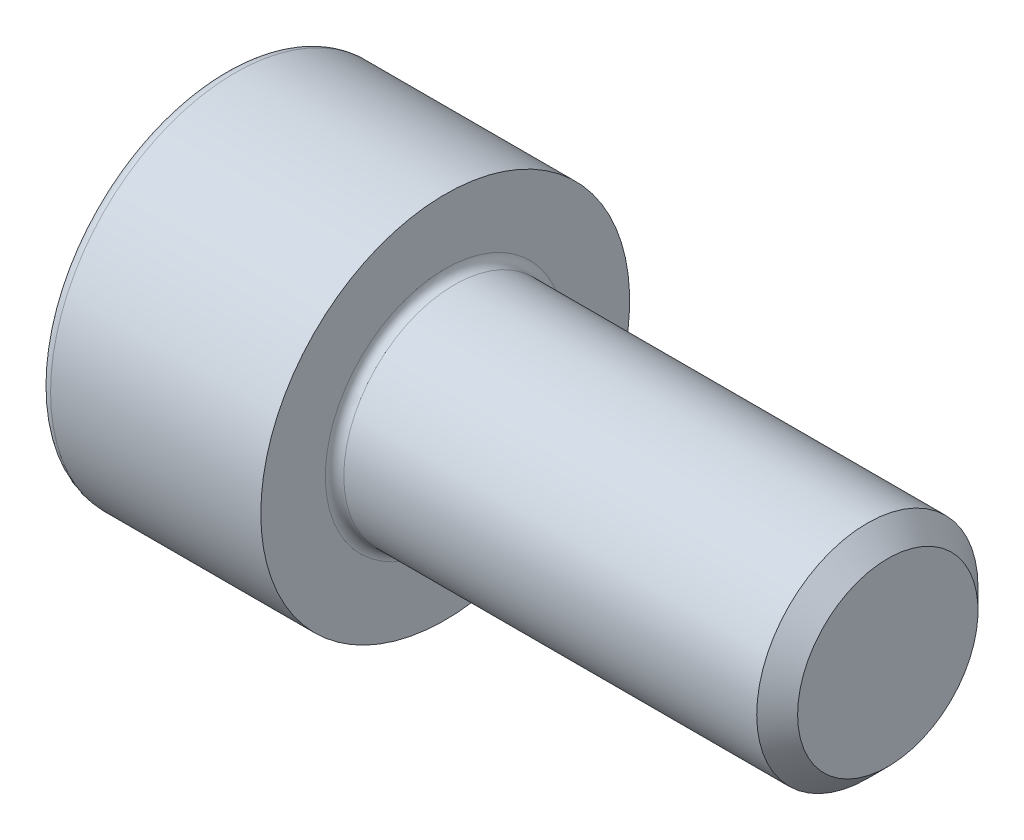
SolidWorks part; units mm, degrees
revolve "Base-Revolve" add sketch "BodySke"
sketch "BodySke" plane through (0, 0, 0) normal (0, 0, 1) x (1, 0, 0)
  line L0 (0, 0) -> (0, 5)
  line L1 (0, 5) -> (6, 5)
  line L2 (6, 5) -> (6, 3)
  line L3 (6, 3) -> (17.4455, 3)
  line L4 (18, 2.4455) -> (18, 0)
  line L5 (18, 0) -> (0, 0)
  line L6 (-31.75, 0) -> (127, 0) construction
  line L8 (18, 2.4455) -> (17.4455, 3)
  line L10 (18, -2.4455) -> (17.4455, -3) construction
  line L11 (7, 9.525) -> (7, 3.175) construction
  line L12 (6, 9.525) -> (6, 3.175) construction
  line L13 (-42, 9.525) -> (-42, 3.175) construction
  dimension "Body_ch_ang" = 45
  dimension "Thread_length" = 60
cosmetic thread "ThreadCosmetic" [suppressed]
fillet "Fillet1" radius 0.25 1 edges at (6, 0, 3)
fillet "Fillet2" radius 0.3 1 edges at (0, 0, 5)
ref_plane "Plane1" through (0, 0, 0) normal (0, 0, 1) x (1, 0, 0)
ref_plane "Plane2" through (0, 0, 0) normal (0, 1, 0) x (1, 0, 0)
ref_plane "Plane3" through (0, 0, 0) normal (1, 0, 0) x (0, 0, -1)
sketch "Sketch2" plane through (0, 0, 0) normal (0, 0, 1) x (1, 0, 0)
  line L0 (0, 2.542) -> (3, 2.542)
  line L1 (3, 2.542) -> (4.4676, 0)
  line L2 (-31.75, 0) -> (127, 0) construction
  line L3 (4.4676, 0) -> (0, 0)
  line L4 (0, 0) -> (0, 2.542)
  line L6 (0, 0) -> (47.625, 0) construction
  dimension "D2" = 60
revolve "Hex-PreBroach" cut sketch "Sketch2" angle 360 about L6
sketch "Sketch3" plane through (0, 0, 0) normal (-1, 0, 0) x (0, 0.5, 0.866)
  line L0 (1.4676, 2.542) -> (-1.4676, 2.542)
  line L1 (-1.4676, 2.542) -> (-2.9352, 0)
  line L2 (1.4676, 2.542) -> (2.9352, 0)
  line L3 (1.4676, -2.542) -> (2.9352, 0)
  line L4 (1.4676, -2.542) -> (-1.4676, -2.542)
  line L5 (-1.4676, -2.542) -> (-2.9352, 0)
extrude "Hex" cut sketch "Sketch3" against normal blind 3
sketch "ThdSchSke" plane through (0, 0, 0) normal (0, 0, 1) x (1, 0, 0)
  line L0 (9, -2.4455) -> (8.6117, -3)
  line L1 (9, -2.4455) -> (9.3883, -3)
  line L2 (9.3883, -3) -> (9.3883, -3.75)
  line L3 (-3.175, 0) -> (5.1513, 0) construction
  line L4 (0, 4.7) -> (0, -4.7) construction
  line L5 (9.3883, -3.75) -> (8.6117, -3.75)
  line L6 (8.6117, -3.75) -> (8.6117, -3)
revolve "ThreadSchematic" [suppressed] cut sketch "ThdSchSke" angle 360 about L3
pattern_linear "ThdSchPat" [suppressed]
equation "\"D2@Sketch3\" = \"Hex_size@Sketch3\" / 2"
equation "\"D1@Sketch3\" = \"Hex_size@Sketch3\" / 2"
equation "\"D1@Sketch2\" = \"Hex_size@Sketch3\" / 2"
equation "\"Thread_minor@ThreadCosmetic\"  =  \"Minor_dia@BodySke\""
equation "\"Depth@Sketch2\" =  \"Key_eng@Hex\""
equation "\"Thread_length@ThreadCosmetic\" = ((sgn( (\"Length@BodySke\" - \"Advance@BodySke\" * 3.0) - \"Thread_nom@BodySke\" )-1)*( (\"Length@BodySke\" - \"Advance@BodySke\" * 3.0) - \"Thread_nom@BodySke\" ))/-2+ \"Thread_nom@BodySke\""
equation "\"Thread_minor@ThdSchSke\" = \"Minor_dia@BodySke\""
equation "\"Diameter@ThdSchSke\" = \"Diameter@BodySke\""
equation "\"Overcut@ThdSchSke\" = \"Diameter@BodySke\" * 1.25"
equation "\"Start@ThdSchSke\" = \"Head_ht@BodySke\" + \"Length@BodySke\" - \"Thread_length@ThreadCosmetic\"  '---Non-countersunk---"
equation "\"Num_threads@ThdSchPat\" = int( \"Thread_length@ThreadCosmetic\" / \"Advance@BodySke\" + 0.999 )  + 1"
equation "\"Advance@ThdSchPat\" = \"Thread_length@ThreadCosmetic\" /  (\"Num_threads@ThdSchPat\" - 1) 'relax it"
equation "\"Num_threads@ThdSchPat\" = \"Num_threads@ThdSchPat\" - sgn( \"Num_threads@ThdSchPat\" - 1) '---chamfered tips only---"
